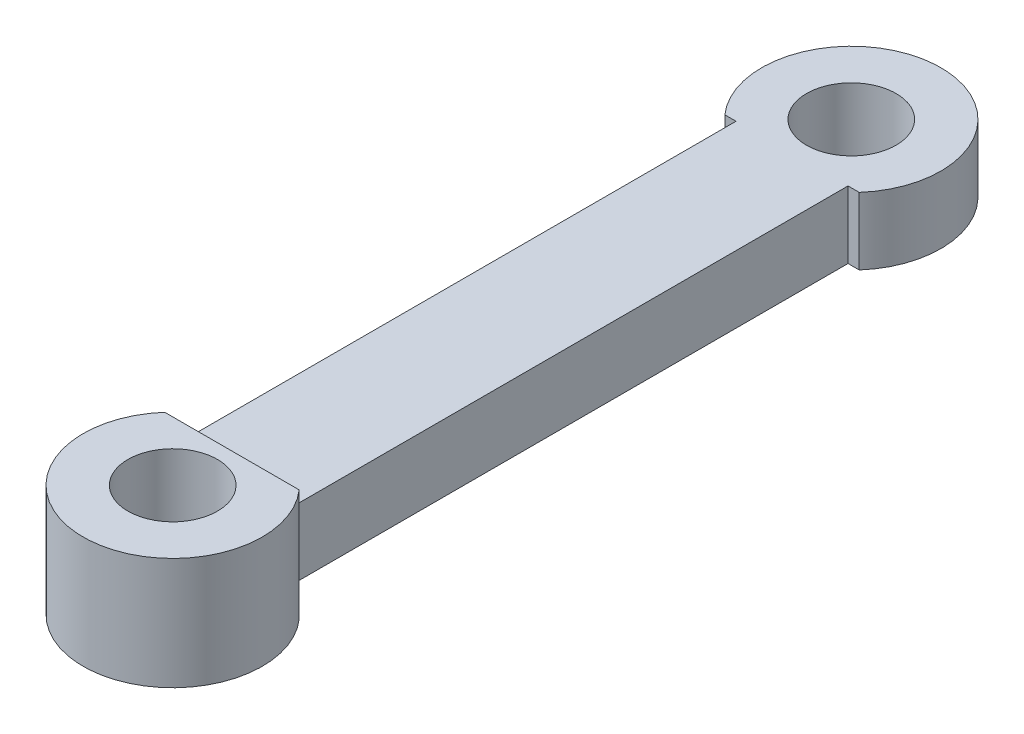
SolidWorks part; units mm, degrees
ref_plane "Front Plane" through (0, 0, 0) normal (0, 0, 1) x (1, 0, 0)
ref_plane "Top Plane" through (0, 0, 0) normal (0, 1, 0) x (1, 0, 0)
ref_plane "Right Plane" through (0, 0, 0) normal (1, 0, 0) x (0, 0, -1)
sketch "Sketch1" plane through (0, 0, 0) normal (0, 1, 0) x (1, 0, 0)
  line L0 (2.5, 12.5) -> (3, 12.5)
  line L5 (-2.5, 12.5) -> (2.5, -12.5) construction
  line L6 (-2.5, -12.5) -> (2.5, 12.5) construction
  line L7 (-2.5, 12.5) -> (-3, 12.5)
  line L11 (-2.5, -12.5) -> (2.5, -12.5)
  line L12 (-2.5, -12.5) -> (-2.5, 12.5)
  line L14 (2.5, -12.5) -> (2.5, 12.5)
  line L15 (-2.5, -12.5) -> (2.5, 12.5) construction
  line L16 (-2.5, 12.5) -> (2.5, -12.5) construction
  arc A4 (-3, 12.5) -> (3, 12.5) centre (0, 15.1458) cw
  circle A5 centre (0, 15.1458) radius 2
  point P0 (0, 0)
  point P15 (0, 0)
  point P19 (0, 0)
  dimension "D3" = 0.5
  dimension "D5" = 4
  dimension "D6" = 4
  dimension "D1" = 25
  dimension "D2" = 5
  dimension "D4" = 0.5
extrude "Boss-Extrude2" add sketch "Sketch1" along normal mid plane 3
sketch "Sketch2" plane through (0, 0, 0) normal (0, 1, 0) x (1, 0, 0)
  line L0 (-2.5, -12.5) -> (2.5, -12.5) construction
  line L1 (-2.5, 12.5) -> (-2.5, -12.5) construction
  line L2 (-3, -12.5) -> (3, -12.5)
  arc A0 (-3, -12.5) -> (3, -12.5) centre (0, -15.1458) ccw
  circle A1 centre (0, -15.1458) radius 2
  point P8 (0, 0)
  point P9 (0, 0)
  point P10 (0, 0)
  dimension "D1" = 4
  dimension "D2" = 4
  dimension "D3" = 6
  dimension "D4" = 0.5
extrude "Boss-Extrude3" add sketch "Sketch2" along normal mid plane 5
